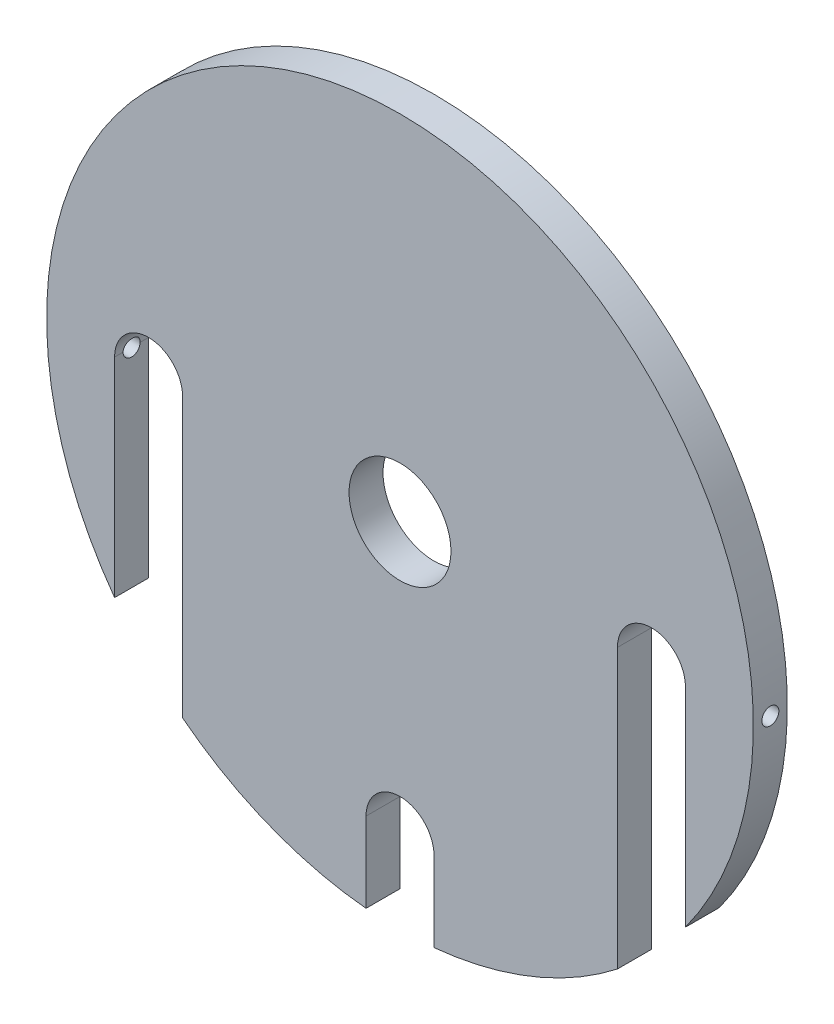
SolidWorks part; units mm, degrees
material "Malleable Cast Iron"
ref_plane "Front Plane" through (0, 0, 0) normal (0, 0, 1) x (1, 0, 0)
ref_plane "Top Plane" through (0, 0, 0) normal (0, 1, 0) x (1, 0, 0)
ref_plane "Right Plane" through (0, 0, 0) normal (1, 0, 0) x (0, 0, -1)
sketch "Sketch1" plane through (0, 0, 0) normal (0, 0, 1) x (1, 0, 0)
  circle A0 centre (0, 0) radius 52
  dimension "D1" = 104
extrude "Boss-Extrude1" add sketch "Sketch1" along normal blind 5
sketch "Sketch2" plane through (0, 0, 5) normal (0, 0, 1) x (1, 0, 0)
  line L0 (0, 0) -> (0, -16.5156) construction
  line L2 (32, 0) -> (32, -45)
  line L3 (32, -45) -> (42, -45)
  line L4 (42, 0) -> (42, -45)
  line L6 (-5, -40) -> (-5, -55)
  line L7 (-5, -55) -> (5, -55)
  line L8 (5, -40) -> (5, -55)
  line L9 (-32, -45) -> (-42, -45)
  line L10 (-42, 0) -> (-42, -45)
  line L12 (-32, 0) -> (-32, -45)
  arc A1 (32, 0) -> (42, 0) centre (37, 0) cw
  arc A2 (-32, 0) -> (-42, 0) centre (-37, 0) ccw
  arc A3 (5, -40) -> (-5, -40) centre (0, -40) ccw
  dimension "D9" = 5
  dimension "D3" = 5
  dimension "D2" = 5
extrude "Cut-Extrude1" cut sketch "Sketch2" against normal blind 10
sketch "Sketch3" plane through (0, 0, 5) normal (0, 0, 1) x (1, 0, 0)
  circle A0 centre (0, 0) radius 7.5
  dimension "D1" = 15
extrude "Cut-Extrude2" cut sketch "Sketch3" against normal blind 10
ref_plane "Plane2" through (52, 0, 0) normal (1, 0, 0) x (0, 0, -1)
hole_wizard "M3 Tapped Hole3" positions "Sketch10" profile "Sketch11" tap size "M3" standard "ISO"
sketch "Sketch10" plane through (52, 0, 0) normal (1, 0, 0) x (0, 0, -1)
  point P0 (-2.5, 0)
  dimension "D1" = 2.5
sketch "Sketch11" plane through (52, 0, 2.5) normal (0, 1, 0) x (0, 0, -1)
  line L0 (0, 0) -> (0, 44.5)
  line L1 (0, 44.5) -> (1.25, 44.5)
  line L2 (1.25, 44.5) -> (1.25, 0)
  line L5 (1.25, 0) -> (0, 0)
  line L11 (0, -6.35) -> (0, 107.95) construction
  dimension "Thru Tap Drill Dia." = 2.5
  dimension "Thru Tap Drill Depth" = 44.5
cosmetic thread "Hole Thread3" parameters "D2"=3
mirror "Mirror1" about plane through (0, 0, 0) normal (1, 0, 0) of "M3 Tapped Hole3"
